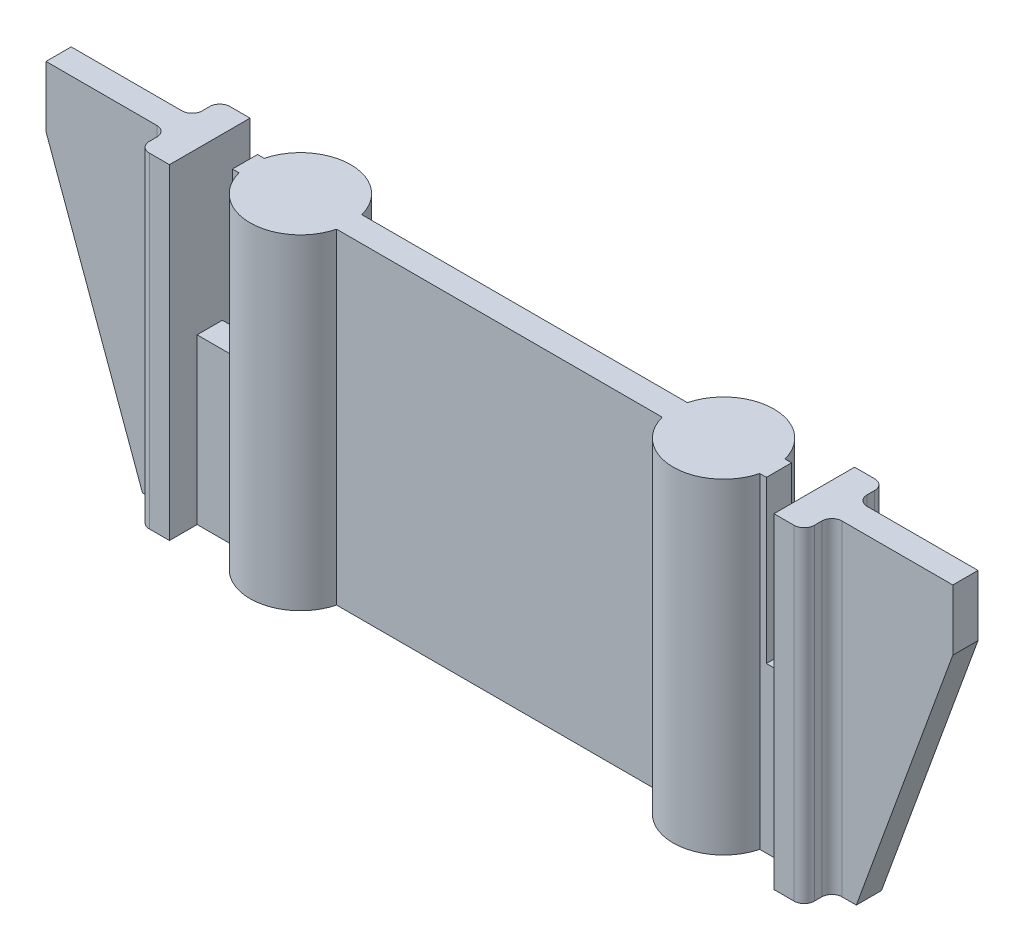
SolidWorks part; units mm, degrees
ref_plane "Front Plane" through (0, 0, 0) normal (0, 0, 1) x (1, 0, 0)
ref_plane "Top Plane" through (0, 0, 0) normal (0, 1, 0) x (1, 0, 0)
ref_plane "Right Plane" through (0, 0, 0) normal (1, 0, 0) x (0, 0, -1)
sketch "Sketch1" plane through (0, 0, 0) normal (0, 1, 0) x (1, 0, 0)
  line L0 (0, 0) -> (0, 10.4261) construction
  line L1 (-27, -17.5) -> (27, -17.5) construction
  line L2 (-27, -17.5) -> (-27, 11.25) construction
  line L3 (-27, 17.5) -> (27, 17.5) construction
  line L4 (27, -17.5) -> (27, 11.25) construction
  line L5 (-27, -17.5) -> (16.5857, 10.75) construction
  line L6 (-27, 17.5) -> (-24.3041, 15.7527) construction
  line L7 (-27, 11.25) -> (-27, 12.75) construction
  line L8 (-45, 13.25) -> (-25.8412, 13.25)
  line L9 (-45, 13.25) -> (-45, 10.75)
  line L10 (-45, 10.75) -> (-25.8412, 10.75)
  line L11 (45, 13.25) -> (45, 10.75)
  line L12 (-45, 13.25) -> (-25.9478, 12.7208) construction
  line L13 (-45, 10.75) -> (-25.9478, 11.2792) construction
  line L14 (-27, 12.75) -> (-27, 17.5) construction
  line L15 (-19.3433, 12.5373) -> (-16.2252, 10.5163) construction
  line L16 (-17.7534, 11.5068) -> (27, -17.5) construction
  line L17 (-16.0198, 12.445) -> (0, 12) construction
  line L18 (17.7534, 11.5068) -> (16.0198, 11.555) construction
  line L19 (0, 12) -> (16.0198, 12.445) construction
  line L20 (25.9478, 12.7208) -> (45, 13.25) construction
  line L21 (16.2252, 10.5163) -> (19.3433, 12.5373) construction
  line L22 (19.3433, 12.5373) -> (20.4429, 13.25) construction
  line L23 (16.0198, 11.555) -> (25.9478, 11.2792) construction
  line L24 (25.9478, 11.2792) -> (45, 10.75) construction
  line L25 (16.5857, 10.75) -> (17.7534, 11.5068) construction
  line L26 (17.7534, 11.5068) -> (16.2252, 10.5163) construction
  line L27 (0, 12) -> (17.7534, 11.5068) construction
  line L28 (-16.2252, 10.5163) -> (-17.7534, 11.5068) construction
  line L29 (-25.8412, 10.75) -> (-16.1588, 10.75) construction
  line L30 (-16.1588, 10.75) -> (16.1588, 10.75)
  line L31 (-25.9478, 11.2792) -> (-16.0198, 11.555) construction
  line L32 (-16.0198, 11.555) -> (0, 12) construction
  line L33 (-25.9478, 12.7208) -> (-19.3433, 12.5373) construction
  line L34 (-19.3433, 12.5373) -> (-16.0198, 12.445) construction
  line L35 (-25.8412, 13.25) -> (-20.4429, 13.25) construction
  line L36 (-16.1588, 13.25) -> (16.1588, 13.25)
  line L37 (-24.3041, 15.7527) -> (-20.4429, 13.25) construction
  line L38 (-20.4429, 13.25) -> (-19.3433, 12.5373) construction
  line L39 (-20.4429, 13.25) -> (-16.1588, 13.25) construction
  line L40 (16.1588, 10.75) -> (10.6337, 10.75) construction
  line L41 (25.8412, 10.75) -> (45, 10.75)
  line L42 (16.0198, 12.445) -> (19.3433, 12.5373) construction
  line L43 (16.1588, 13.25) -> (20.4429, 13.25) construction
  line L44 (25.8412, 13.25) -> (45, 13.25)
  line L45 (20.4429, 13.25) -> (24.3041, 15.7527) construction
  line L46 (24.3041, 15.7527) -> (27, 17.5) construction
  line L47 (20.4429, 13.25) -> (25.8412, 13.25) construction
  line L48 (19.3433, 12.5373) -> (45, 13.25) construction
  line L49 (27, 11.25) -> (27, 12.75) construction
  line L50 (27, 12.75) -> (27, 17.5) construction
  arc A0 (16.2252, 10.5163) -> (25.8412, 10.75) centre (21, 12) ccw construction
  arc A1 (-25.8412, 10.75) -> (-16.1588, 10.75) centre (-21, 12) ccw
  arc A2 (-25.9478, 12.7208) -> (-25.9478, 11.2792) centre (-21, 12) ccw construction
  arc A3 (-16.2252, 10.5163) -> (-16.0198, 11.555) centre (-21, 12) ccw construction
  arc A4 (-16.1588, 13.25) -> (-25.8412, 13.25) centre (-21, 12) ccw
  arc A5 (16.0198, 12.445) -> (16.2252, 10.5163) centre (21, 12) ccw construction
  arc A6 (16.1588, 13.25) -> (16.0198, 12.445) centre (21, 12) ccw construction
  arc A7 (16.0198, 11.555) -> (16.1588, 10.75) centre (21, 12) ccw construction
  arc A8 (16.1588, 10.75) -> (25.8412, 10.75) centre (21, 12) ccw
  arc A9 (-16.1588, 10.75) -> (-16.0198, 11.555) centre (-21, 12) ccw construction
  arc A10 (-16.1588, 13.25) -> (-25.8412, 13.25) centre (-21, 12) ccw construction
  arc A11 (25.9478, 11.2792) -> (25.9478, 12.7208) centre (21, 12) ccw construction
  arc A12 (25.8412, 13.25) -> (16.1588, 13.25) centre (21, 12) ccw
  arc A13 (25.9478, 12.7208) -> (25.8412, 13.25) centre (21, 12) ccw construction
  arc A14 (25.8412, 10.75) -> (25.9478, 11.2792) centre (21, 12) ccw construction
  arc A15 (25.9478, 11.2792) -> (16.0198, 11.555) centre (21, 12) ccw construction
  arc A16 (25.8412, 10.75) -> (25.9478, 11.2792) centre (21, 12) ccw construction
  arc A17 (-25.9478, 11.2792) -> (-25.8412, 10.75) centre (-21, 12) ccw construction
  arc A18 (-25.8412, 10.75) -> (-16.2252, 10.5163) centre (-21, 12) ccw construction
  arc A19 (-25.9478, 11.2792) -> (-25.8412, 10.75) centre (-21, 12) ccw construction
  arc A20 (-25.8412, 13.25) -> (-25.9478, 12.7208) centre (-21, 12) ccw construction
  arc A21 (-25.9478, 12.7208) -> (-25.9478, 11.2792) centre (-21, 12) ccw construction
  arc A22 (-25.8412, 13.25) -> (-25.9478, 12.7208) centre (-21, 12) ccw construction
  arc A23 (-16.0198, 11.555) -> (-16.0198, 12.445) centre (-21, 12) ccw construction
  arc A24 (-16.0198, 11.555) -> (-16.0198, 12.445) centre (-21, 12) ccw construction
  arc A25 (-16.0198, 12.445) -> (-16.1588, 13.25) centre (-21, 12) ccw construction
  arc A26 (-16.0198, 12.445) -> (-16.1588, 13.25) centre (-21, 12) ccw construction
  point P4 (0, 0)
  point P13 (0, 12)
  dimension "D1" = 10
  dimension "D2" = 2.5
  dimension "D3" = 54
  dimension "D4" = 35
  dimension "D5" = 42
  dimension "D6" = 90
  dimension "D7" = 12
extrude "Boss-Extrude1" add sketch "Sketch1" along normal blind 32.31 contours A4 L8 L9 L10 A1 L30 A8 L41 L11 L44 A12 L36
sketch "Sketch2" plane through (0, 0, -10.75) normal (0, 0, 1) x (1, 0, 0)
  line L0 (-35.4206, 0) -> (-45, 26.2724)
  line L1 (-45, 0) -> (-25.8412, 0) construction
  line L2 (-45, 32.31) -> (-45, 0) construction
  line L3 (-45, 26.2724) -> (-58.3904, 22.5254)
  line L4 (-58.3904, 22.5254) -> (-53.8147, -5.5007)
  line L5 (-53.8147, -5.5007) -> (-35.4206, -4.7634)
  line L6 (-35.4206, -4.7634) -> (-35.4206, 0)
  line L7 (0, 0) -> (0, 6.7705) construction
  line L8 (-16.1588, 0) -> (16.1588, 0) construction
  line L9 (53.8147, -5.5007) -> (35.4206, -4.7634)
  line L10 (58.3904, 22.5254) -> (53.8147, -5.5007)
  line L11 (45, 26.2724) -> (58.3904, 22.5254)
  line L12 (35.4206, 0) -> (45, 26.2724)
  line L13 (35.4206, -4.7634) -> (35.4206, 0)
extrude "Cut-Extrude1" cut sketch "Sketch2" against normal blind 25
sketch "Sketch3" plane through (0, 32.31, 0) normal (0, 1, 0) x (1, 0, 0)
  line L0 (0, 0) -> (0, 18.923) construction
  line L1 (-30, 3.9506) -> (-26.5, 3.9506)
  line L2 (-30, 3.9506) -> (-30, 20.1133)
  line L3 (-30, 20.1133) -> (-26.5, 20.1133)
  line L4 (-26.5, 3.9506) -> (-26.5, 20.1133)
  line L5 (-30, 3.9506) -> (-26.5, 20.1133) construction
  line L6 (-30, 20.1133) -> (-26.5, 3.9506) construction
  line L7 (30, 20.1133) -> (26.5, 20.1133)
  line L8 (26.5, 3.9506) -> (26.5, 20.1133)
  line L9 (30, 3.9506) -> (26.5, 3.9506)
  line L10 (30, 3.9506) -> (30, 20.1133)
  point P0 (-28.25, 12.032)
  dimension "D1" = 3.5
  dimension "D2" = 60
extrude "Cut-Extrude2" cut sketch "Sketch3" against normal blind 16
sketch "Sketch4" plane through (0, 0, 0) normal (0, -1, 0) x (1, 0, 0)
  line L1 (-33, -16) -> (-30, -16)
  line L2 (-33, -16) -> (-33, -8)
  line L3 (-33, -8) -> (-30, -8)
  line L4 (-30, -16) -> (-30, -8)
  line L5 (-33, -16) -> (-30, -8) construction
  line L6 (-33, -8) -> (-30, -16) construction
  line L7 (-35.4206, -12) -> (-14.4349, -12) construction
  line L8 (-35.4206, -10.75) -> (-35.4206, -13.25) construction
  line L9 (-30, -13.25) -> (-30, -10.75) construction
  point P0 (-31.5, -12)
  dimension "D1" = 3
  dimension "D2" = 8
extrude "Boss-Extrude2" add sketch "Sketch4" against normal up to surface (32.31 mm away) up to face at (-37.5, 32.31, -12)
fillet "Fillet1" radius 1 4 edges at (-33, 16.155, -16) (-33, 16.155, -8) (-33, 16.155, -10.75) (-33, 16.155, -13.25)
mirror "Mirror1" about plane through (0, 0, 0) normal (1, 0, 0) of "Boss-Extrude2"
fillet "Fillet2" radius 1 4 edges at (33, 16.155, -16) (33, 16.155, -13.25) (33, 16.155, -10.75) (33, 16.155, -8)
hole_wizard "M3 Clearance Hole1" positions "Sketch5" profile "Sketch6" hole size "M3" standard "ANSI Metric"
sketch "Sketch5" plane through (0, 0, 0) normal (0, -1, 0) x (-1, 0, 0)
  circle A0 centre (-21, 12) radius 5.6035 construction
  arc A1 (-16.1588, 13.25) -> (-25.8412, 13.25) centre (-21, 12) ccw construction
  arc A2 (25.8412, 13.25) -> (16.1588, 13.25) centre (21, 12) ccw construction
  point P0 (-21, 12)
  point P2 (21, 12)
sketch "Sketch6" plane through (21, 0, -12) normal (1, 0, 0) x (0, 0, -1)
  line L0 (0, 0) -> (0, 17.0815)
  line L1 (0, 17.0815) -> (1.8, 16)
  line L2 (1.8, 16) -> (1.8, 0)
  line L5 (1.8, 0) -> (0, 0)
  line L10 (0, 17.0815) -> (-1.8, 16) construction
  line L11 (0, -6.35) -> (0, 107.95) construction
  dimension "Hole Dia." = 3.6
  dimension "Hole Depth" = 16
  dimension "Drill Angle" = 118
ref_plane "Plane1" through (0, 10, 0) normal (0, -1, 0) x (-1, 0, 0)
sketch "Sketch7" plane through (0, 10, 0) normal (0, -1, 0) x (-1, 0, 0)
  line L1 (-21, 15.6373) -> (-24.15, 13.8187) construction
  line L2 (-24.15, 13.8187) -> (-24.15, 10.1813)
  line L3 (-24.15, 10.1813) -> (-21, 8.3627)
  line L4 (-21, 8.3627) -> (-17.85, 10.1813)
  line L5 (-17.85, 10.1813) -> (-17.85, 13.8187)
  line L6 (-17.85, 13.8187) -> (-21, 15.6373) construction
  line L7 (-24.15, 13.8187) -> (-17.85, 13.8187) construction
  line L8 (-24.15, 13.8187) -> (-24.15, 20.1574)
  line L9 (-24.15, 20.1574) -> (-17.85, 20.1574)
  line L10 (-17.85, 13.8187) -> (-17.85, 20.1574)
  circle A0 centre (-21, 12) radius 3.15 construction
  dimension "D1" = 6.3
extrude "Cut-Extrude3" cut sketch "Sketch7" along normal blind 4
mirror "Mirror2" about plane through (0, 0, 0) normal (1, 0, 0) of "Cut-Extrude3"
